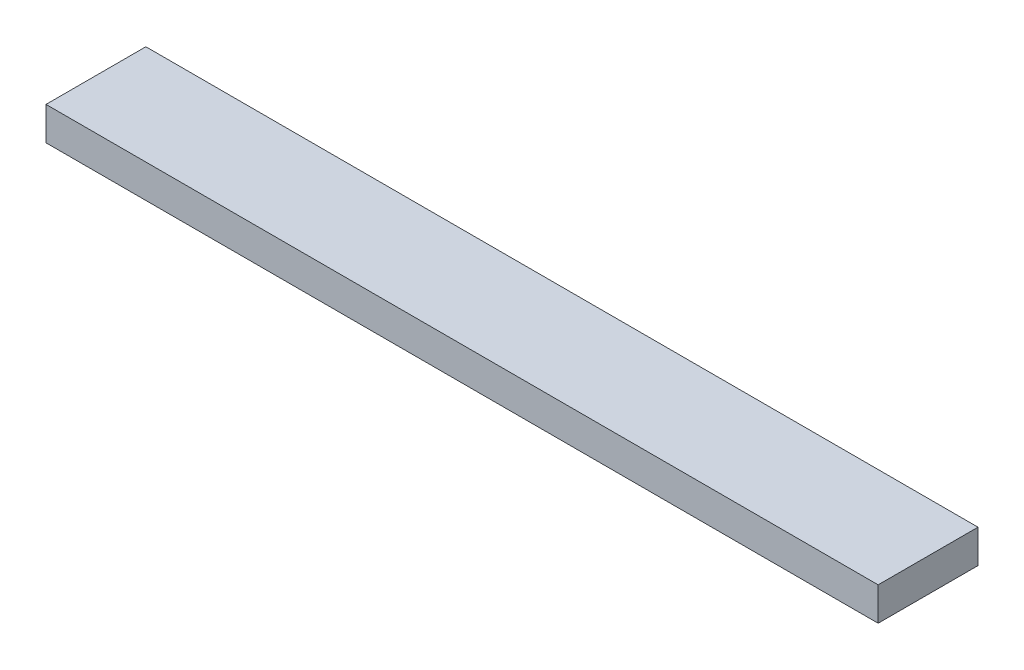
SolidWorks part; units mm, degrees
ref_plane "Front Plane" through (0, 0, 0) normal (0, 0, 1) x (1, 0, 0)
ref_plane "Top Plane" through (0, 0, 0) normal (0, 1, 0) x (1, 0, 0)
ref_plane "Right Plane" through (0, 0, 0) normal (1, 0, 0) x (0, 0, -1)
sketch "Sketch1" plane through (0, 0, 0) normal (0, 1, 0) x (1, 0, 0)
  line L1 (-250, -30) -> (250, -30)
  line L2 (-250, -30) -> (-250, 30)
  line L3 (-250, 30) -> (250, 30)
  line L4 (250, -30) -> (250, 30)
  line L5 (-250, -30) -> (250, 30) construction
  line L6 (-250, 30) -> (250, -30) construction
  point P0 (0, 0)
  dimension "D1" = 500
  dimension "D2" = 60
extrude "Boss-Extrude1" add sketch "Sketch1" along normal blind 20
